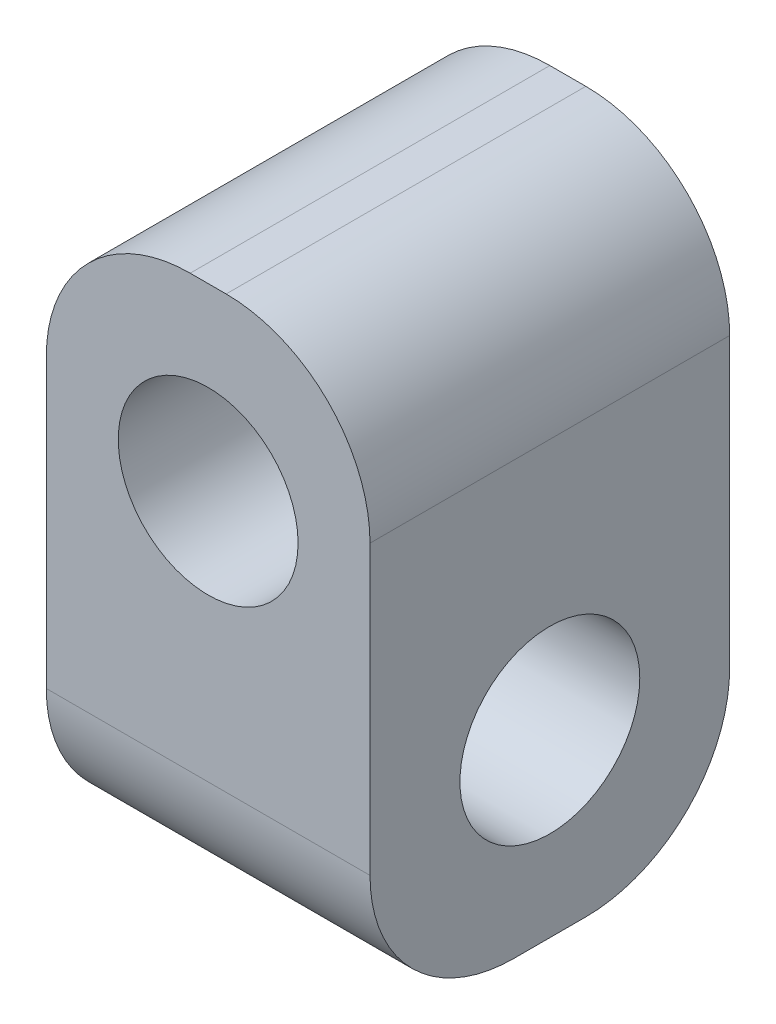
SolidWorks part; units mm, degrees
ref_plane "Front Plane" through (0, 0, 0) normal (0, 0, 1) x (1, 0, 0)
ref_plane "Top Plane" through (0, 0, 0) normal (0, 1, 0) x (1, 0, 0)
ref_plane "Right Plane" through (0, 0, 0) normal (1, 0, 0) x (0, 0, -1)
sketch "Sketch1" plane through (0, 0, 0) normal (0, 0, 1) x (1, 0, 0)
  line L1 (-2.5, 25) -> (2.5, 25)
  line L2 (22.5, 5) -> (22.5, -15)
  line L3 (22.5, -15) -> (-22.5, -15)
  line L5 (-22.5, -15) -> (-22.5, 5)
  circle A0 centre (0, 0) radius 12.5
  arc A1 (22.5, 5) -> (2.5, 25) centre (2.5, 5) ccw
  arc A2 (-2.5, 25) -> (-22.5, 5) centre (-2.5, 5) ccw
  point P7 (0, 25)
  point P11 (22.5, 25)
  point P14 (-22.5, 25)
  dimension "D3" = 20
  dimension "D5" = 25
  dimension "D1" = 22.5
  dimension "D2" = 40
  dimension "D4" = 45
  dimension "D6" = 25
extrude "Boss-Extrude1" add sketch "Sketch1" along normal blind 50
sketch "Sketch2" plane through (0, 0, 0) normal (1, 0, 0) x (0, 0, -1)
  line L0 (-50, -15) -> (-50, -35)
  line L1 (-30, -55) -> (-20, -55)
  line L2 (0, -35) -> (0, -15)
  line L5 (-50, -15) -> (0, -15)
  circle A0 centre (-25, -30) radius 12.5
  arc A1 (0, -35) -> (-20, -55) centre (-20, -35) cw
  arc A2 (-50, -35) -> (-30, -55) centre (-30, -35) ccw
  point P12 (-50, -55)
  dimension "D2" = 20
  dimension "D5" = 25
  dimension "D1" = 40
  dimension "D3" = 50
  dimension "D4" = 25
  dimension "D6" = 25
extrude "Boss-Extrude2" add sketch "Sketch2" along normal mid plane 45
